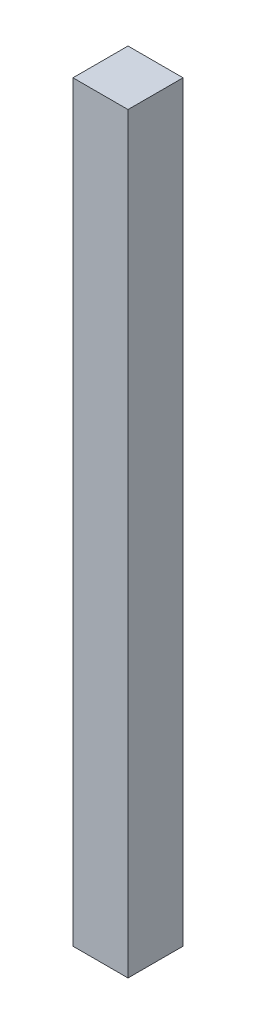
SolidWorks part; units mm, degrees
ref_plane "Front Plane" through (0, 0, 0) normal (0, 0, 1) x (1, 0, 0)
ref_plane "Top Plane" through (0, 0, 0) normal (0, 1, 0) x (1, 0, 0)
ref_plane "Right Plane" through (0, 0, 0) normal (1, 0, 0) x (0, 0, -1)
sketch "Sketch1" plane through (0, 0, 0) normal (0, 1, 0) x (1, 0, 0)
  line L1 (0, 0) -> (38.1, 0)
  line L2 (0, 0) -> (0, -38.1)
  line L3 (0, -38.1) -> (38.1, -38.1)
  line L4 (38.1, 0) -> (38.1, -38.1)
extrude "Boss-Extrude1" add sketch "Sketch1" along normal blind 520.7
